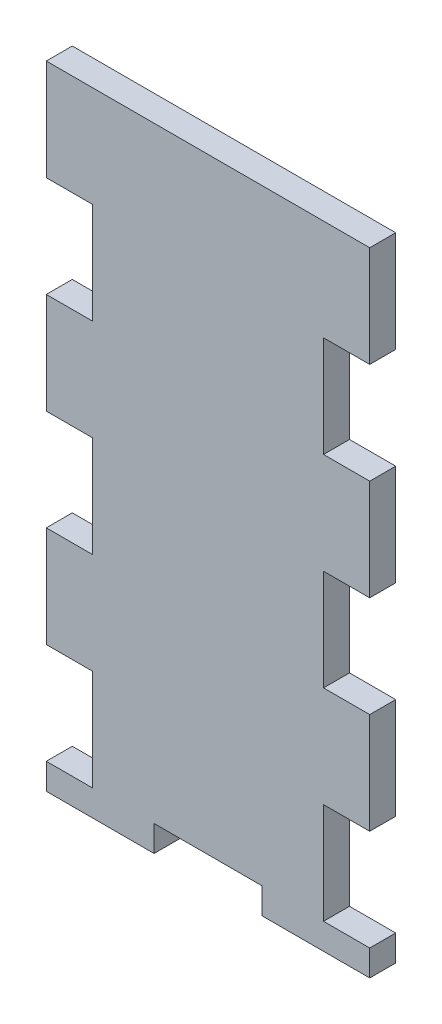
SolidWorks part; units mm, degrees
ref_plane "Front Plane" through (0, 0, 0) normal (0, 0, 1) x (1, 0, 0)
ref_plane "Top Plane" through (0, 0, 0) normal (0, 1, 0) x (1, 0, 0)
ref_plane "Right Plane" through (0, 0, 0) normal (1, 0, 0) x (0, 0, -1)
sketch "Sketch1" plane through (0, 0, 0) normal (0, 0, 1) x (1, 0, 0)
  line L0 (24, 61.25) -> (24, 52.5) construction
  line L1 (0, 0) -> (20, 0)
  line L2 (0, 0) -> (0, 70)
  line L3 (0, 70) -> (20, 70)
  line L4 (20, 0) -> (20, 70)
  line L13 (20, 70) -> (24, 70)
  line L18 (20, 70) -> (20, 61.25)
  line L19 (10, 0) -> (10, 70) construction
  line L20 (20, 61.25) -> (24, 61.25)
  line L21 (24, 70) -> (24, 61.25)
  line L42 (20, 52.5) -> (24, 52.5)
  line L43 (20, 52.5) -> (20, 43.75)
  line L44 (20, 43.75) -> (24, 43.75)
  line L45 (24, 52.5) -> (24, 43.75)
  line L46 (24, 43.75) -> (24, 35) construction
  line L47 (20, 35) -> (24, 35)
  line L48 (20, 35) -> (20, 26.25)
  line L49 (20, 26.25) -> (24, 26.25)
  line L50 (24, 35) -> (24, 26.25)
  line L51 (24, 26.25) -> (24, 17.5) construction
  line L52 (20, 17.5) -> (24, 17.5)
  line L53 (20, 17.5) -> (20, 8.75)
  line L54 (20, 8.75) -> (24, 8.75)
  line L55 (24, 17.5) -> (24, 8.75)
  line L56 (24, 8.75) -> (24, 0) construction
  line L57 (-4, 26.25) -> (-4, 17.5) construction
  line L58 (-4, 43.75) -> (-4, 35) construction
  line L59 (-4, 61.25) -> (-4, 52.5) construction
  line L60 (-4, 17.5) -> (-4, 8.75)
  line L61 (0, 8.75) -> (-4, 8.75)
  line L62 (0, 17.5) -> (0, 8.75)
  line L63 (0, 17.5) -> (-4, 17.5)
  line L64 (-4, 35) -> (-4, 26.25)
  line L65 (0, 26.25) -> (-4, 26.25)
  line L66 (0, 35) -> (0, 26.25)
  line L67 (0, 35) -> (-4, 35)
  line L68 (-4, 52.5) -> (-4, 43.75)
  line L69 (0, 43.75) -> (-4, 43.75)
  line L70 (0, 52.5) -> (0, 43.75)
  line L71 (0, 52.5) -> (-4, 52.5)
  line L72 (-4, 70) -> (-4, 61.25)
  line L73 (0, 61.25) -> (-4, 61.25)
  line L74 (0, 70) -> (0, 61.25)
  line L75 (0, 70) -> (-4, 70)
  dimension "D1" = 20
  dimension "D2" = 70
  dimension "D4" = 4
  dimension "D3" = 4
extrude "Boss-Extrude1" add sketch "Sketch1" along normal blind 2.25
sketch "Sketch2" plane through (0, 0, 0) normal (0, 0, -1) x (-1, 0, 0)
  line L0 (0, 0) -> (-20, 0) construction
  line L1 (4, 0) -> (-24, 0)
  line L2 (4, 0) -> (4, -2.25)
  line L3 (4, -2.25) -> (-24, -2.25)
  line L4 (-24, 0) -> (-24, -2.25)
  line L6 (-24, 17.5) -> (-24, 8.75) construction
  line L7 (4, 17.5) -> (4, 8.75) construction
  dimension "D1" = 2.25
extrude "Boss-Extrude2" add sketch "Sketch2" against normal up to surface (2.25 mm away) up to face at (10, 35, 2.25)
sketch "Sketch3" plane through (0, 0, 2.25) normal (0, 0, 1) x (1, 0, 0)
  line L0 (24, -2.25) -> (-4, -2.25) construction
  line L1 (14.6667, -2.25) -> (5.3333, -2.25)
  line L2 (14.6667, -2.25) -> (14.6667, 0)
  line L3 (14.6667, 0) -> (5.3333, 0)
  line L4 (5.3333, -2.25) -> (5.3333, 0)
  line L5 (10, -2.25) -> (10, 70) construction
  line L6 (-4, 70) -> (24, 70) construction
  line L7 (14.6667, 0) -> (24, 0) construction
  line L8 (24, 0) -> (24, -2.25) construction
  line L9 (5.3333, 0) -> (-4, 0) construction
  line L10 (-4, -2.25) -> (-4, 0) construction
  line L11 (20, 0) -> (24, 0) construction
  point P6 (10, 0)
extrude "Cut-Extrude1" cut sketch "Sketch3" against normal through all
sketch "Sketch4" plane through (0, 0, 2.25) normal (0, 0, 1) x (1, 0, 0)
  line L0 (0, 61.25) -> (-4, 61.25) construction
  line L1 (-4, 70) -> (-1.75, 70)
  line L2 (-4, 70) -> (-4, 61.25)
  line L3 (-4, 61.25) -> (-1.75, 61.25)
  line L4 (-1.75, 70) -> (-1.75, 61.25)
  line L5 (20, 61.25) -> (24, 61.25) construction
  line L6 (24, 70) -> (21.75, 70)
  line L7 (24, 70) -> (24, 61.25)
  line L8 (24, 61.25) -> (21.75, 61.25)
  line L9 (21.75, 70) -> (21.75, 61.25)
  dimension "D1" = 2.25
extrude "Cut-Extrude2" cut sketch "Sketch4" against normal through all
sketch "Sketch5" plane through (0, 0, 2.25) normal (0, 0, 1) x (1, 0, 0)
  line L1 (-4, 52.5) -> (24, 52.5)
  line L2 (-4, 52.5) -> (-4, 70)
  line L3 (-4, 70) -> (24, 70)
  line L4 (24, 52.5) -> (24, 70)
  line L5 (-1.75, 70) -> (21.75, 70) construction
extrude "Cut-Extrude3" cut sketch "Sketch5" against normal through all
equation "\"D1@Boss-Extrude1\"=\"thick\"+\"veneer_thickness\""
equation "\"D4@Sketch1\"=\"thick\"*2 + \"veneer_thickness\""
equation "\"D1@Sketch2\"=\"thick\" + \"veneer_thickness\""
equation "\"D1@Sketch4\"=\"thick\"+\"veneer_thickness\""
equation "\"veneer_thickness\"= 0.5mm"
equation "\"thick\"= 1.75mm"
